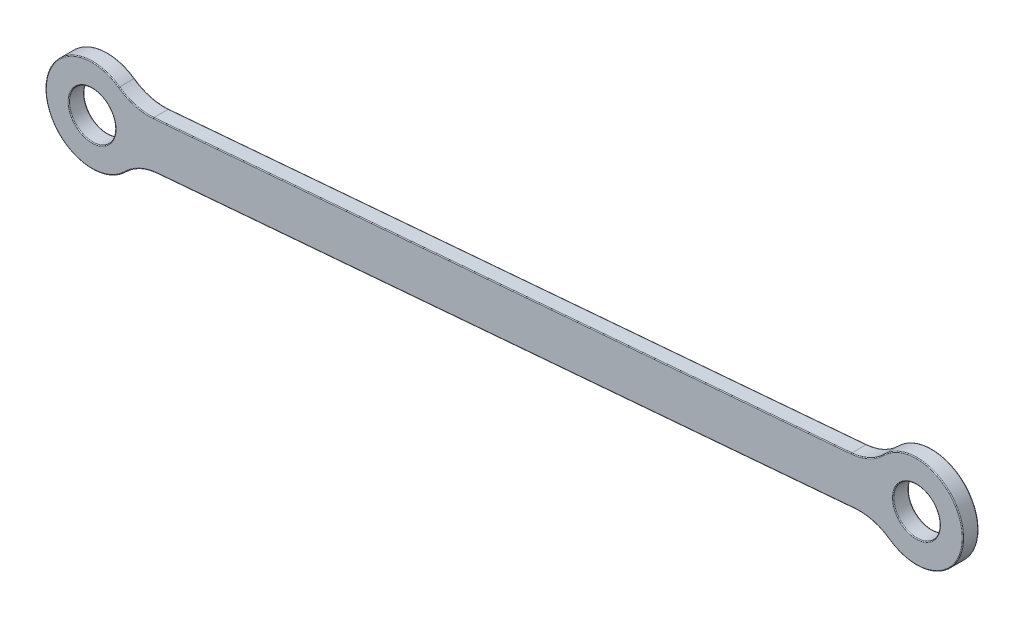
SolidWorks part; units mm, degrees
ref_plane "Płaszczyzna przednia" through (0, 0, 0) normal (0, 0, 1) x (1, 0, 0)
ref_plane "Płaszczyzna górna" through (0, 0, 0) normal (0, 1, 0) x (1, 0, 0)
ref_plane "Płaszczyzna prawa" through (0, 0, 0) normal (1, 0, 0) x (0, 0, -1)
sketch "Szkic1" plane through (0, 0, 0) normal (0, 0, 1) x (1, 0, 0)
  line L0 (-86.9251, 226.2774) -> (-246.3656, 212.909) construction
  line L1 (-86.9251, 226.2774) -> (-246.3656, 212.909) construction
sketch "Szkic2" plane through (0, 0, 0) normal (0, 0, 1) x (1, 0, 0)
  line L0 (-246.3656, 212.909) -> (-86.9251, 226.2774) construction
  line L1 (-86.9251, 226.2774) -> (-246.3656, 212.909) construction
  line L2 (-246.7416, 217.3933) -> (-87.301, 230.7616)
  line L3 (-245.9896, 208.4248) -> (-86.5491, 221.7931)
  arc A0 (-246.7416, 217.3933) -> (-245.9896, 208.4248) centre (-246.3656, 212.909) ccw
  arc A1 (-86.5491, 221.7931) -> (-87.301, 230.7616) centre (-86.9251, 226.2774) ccw
  circle A2 centre (-86.9251, 226.2774) radius 9
  circle A3 centre (-246.3656, 212.909) radius 9
  arc A4 (-246.7416, 217.3933) -> (-245.9896, 208.4248) centre (-246.3656, 212.909) cw
  arc A5 (-86.9251, 230.7774) -> (-86.5491, 221.7931) centre (-86.9251, 226.2774) ccw
  point P5 (-166.6453, 219.5932)
  dimension "D3" = 18
  dimension "D1" = 9
extrude "Dodanie-wyciągnięcie1" add sketch "Szkic2" along normal blind 3 contours L2 A3 L3 A0 | L0 A4 L3 A3 | A4 L0 A3 L2 | A3 L0 A2 L2 | L0 A3 L3 A2 | L0 A2 L3 A5 | A2 L0 A5 L2 | L3 A2 L2 A1
fillet "Zaokrąglenie1" radius 10 1 edges at (-238.9746, 218.0445, 1.5)
fillet "Zaokrąglenie2" radius 10 1 edges at (-238.2226, 209.076, 1.5)
fillet "Zaokrąglenie3" radius 10 1 edges at (-95.068, 230.1104, 1.5)
fillet "Zaokrąglenie4" radius 10 1 edges at (-94.316, 221.1419, 1.5)
fillet "Zaokrąglenie5" radius 0.15 20 edges at (-241.8656, 212.909, 3) (-241.8656, 212.909, 0) (-96.158, 230.6319, 3) (-96.158, 230.6319, 0) (-167.0213, 224.0775, 3) (-167.0213, 224.0775, 0) (-237.9867, 218.7403, 3) (-237.9867, 218.7403, 0) (-255.3341, 212.1571, 0) (-255.3341, 212.1571, 3) (-237.1327, 208.5545, 3) (-237.1327, 208.5545, 0) (-166.2693, 215.1089, 0) (-166.2693, 215.1089, 3) (-95.3039, 220.4461, 3) (-95.3039, 220.4461, 0) (-77.9565, 227.0293, 3) (-77.9565, 227.0293, 0) (-82.4251, 226.2774, 3) (-82.4251, 226.2774, 0)
